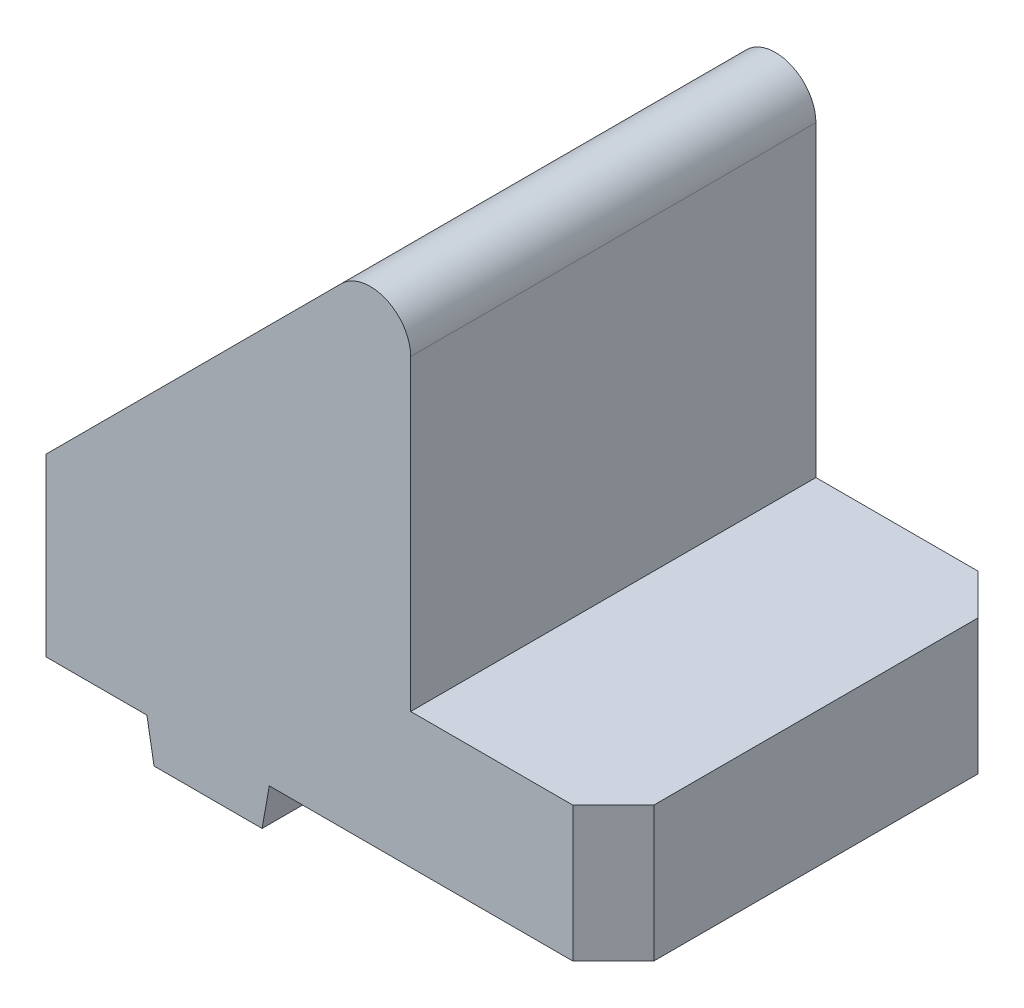
SolidWorks part; units mm, degrees
ref_plane "Alzado" through (0, 0, 0) normal (0, 0, 1) x (1, 0, 0)
ref_plane "Planta" through (0, 0, 0) normal (0, 1, 0) x (1, 0, 0)
ref_plane "Vista lateral" through (0, 0, 0) normal (1, 0, 0) x (0, 0, -1)
sketch "Croquis1" plane through (0, 0, 0) normal (0, 0, 1) x (1, 0, 0)
  line L0 (0, 0) -> (-30, 0) construction
  line L1 (-30, 0) -> (-30, 10)
  line L2 (-30, 10) -> (0, 40)
  line L3 (0, 40) -> (0, 10)
  line L4 (0, 10) -> (15, 10)
  line L5 (15, 10) -> (15, 0)
  line L6 (15, 0) -> (0, 0)
  line L7 (-15, 0) -> (-15, 50000) construction
  line L8 (-10.471, 0) -> (-11, -3)
  line L9 (-19, -3) -> (-11, -3)
  line L10 (-19, -3) -> (-19.529, 0)
  line L11 (-10.471, 0) -> (0, 0)
  line L12 (-19.529, 0) -> (-30, 0)
  point P10 (-15, 0)
  point P13 (-15, -3)
  dimension "D1" = 30
  dimension "D2" = 15
  dimension "D3" = 10
  dimension "D4" = 30
  dimension "D5" = 3
  dimension "D6" = 8
  dimension "D7" = 80
extrude "Saliente-Extruir1" add sketch "Croquis1" along normal mid plane 30
chamfer "Chaflán1" distance 3 angle 45 4 edges at (15, 5, -15) (15, 5, 15) (-30, 5, 15) (-30, 5, -15)
sketch "Croquis3" plane through (0, 0, 0) normal (0, -1, 0) x (1, 0, 0)
  line L0 (0, 0) -> (-50000, 0) construction
  line L1 (-15, 0) -> (-15, 50000) construction
  line L2 (0, 15) -> (0, -15) construction
  line L4 (-7, 8) -> (-23, 8)
  line L5 (-7, 8) -> (-7, -8)
  line L6 (-7, -8) -> (-23, -8)
  line L7 (-23, 8) -> (-23, -8)
  line L8 (-7, 8) -> (-23, -8) construction
  line L9 (-7, -8) -> (-23, 8) construction
  point P7 (-15, 0)
  dimension "D1" = 15
  dimension "D2" = 16
  dimension "D3" = 16
extrude "Cortar-Extruir1" cut sketch "Croquis3" against normal through all from offset 10 offset against normal yes
chamfer "Chaflán2" distance 3 angle 45 4 edges at (-23, 13.5, 8) (-7, 21.5, 8) (-7, 21.5, -8) (-23, 13.5, -8)
sketch "Croquis4" plane through (0, 10, 0) normal (0, 1, 0) x (1, 0, 0)
  circle A0 centre (-15, 0) radius 3.2
  dimension "D1" = 6.4
extrude "Cortar-Extruir2" cut sketch "Croquis4" against normal through all
fillet "Redondeo1" radius 3 1 edges at (0, 40, 0)
